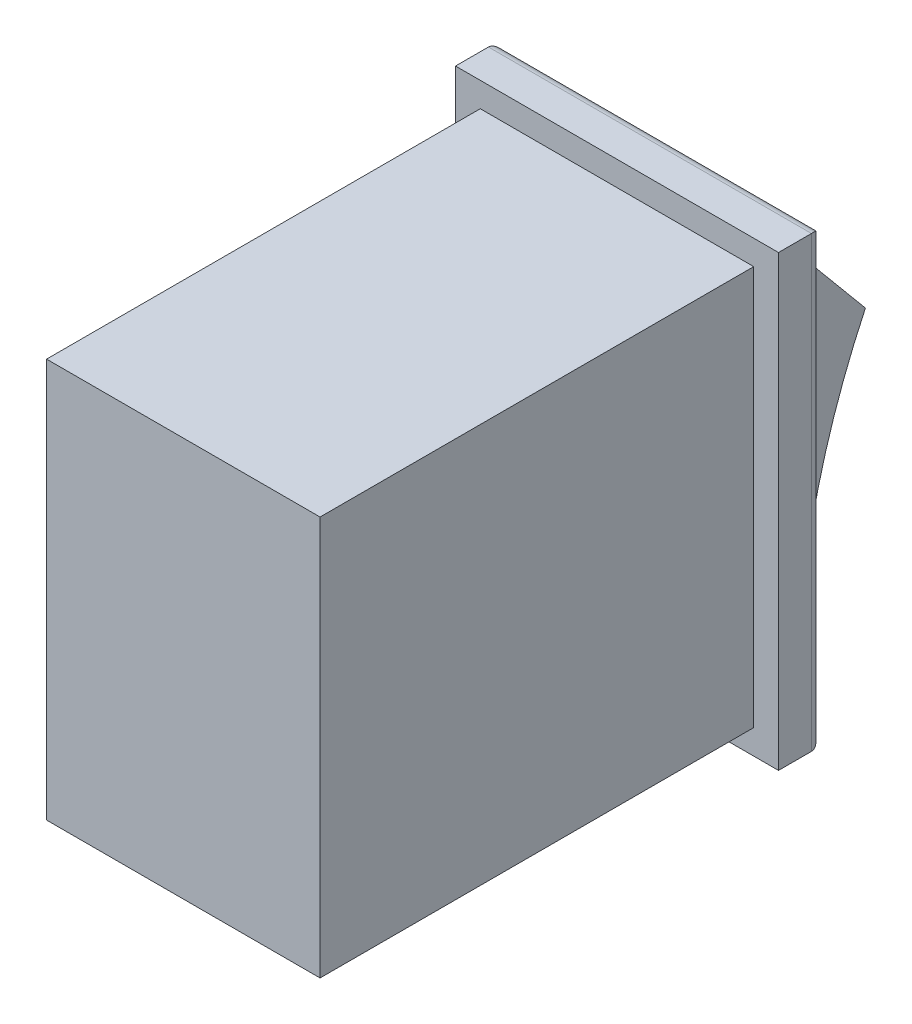
SolidWorks part; units mm, degrees
ref_plane "Front" through (0, 0, 0) normal (0, 0, 1) x (1, 0, 0)
ref_plane "Top" through (0, 0, 0) normal (0, 1, 0) x (1, 0, 0)
ref_plane "Right" through (0, 0, 0) normal (1, 0, 0) x (0, 0, -1)
sketch "Sketch1" plane through (0, 0, 0) normal (0, 0, 1) x (1, 0, 0)
  line L1 (0, 0) -> (12.7, 0)
  line L2 (0, 0) -> (0, -18.54)
  line L3 (0, -18.54) -> (12.7, -18.54)
  line L4 (12.7, 0) -> (12.7, -18.54)
  dimension "D1" = 12.7
  dimension "D2" = 18.54
extrude "Extrude1" add sketch "Sketch1" along normal blind 20.14
sketch "Sketch2" plane through (0, 0, 0) normal (0, 0, -1) x (-1, 0, 0)
  line L0 (0, 0) -> (0, -18.54) construction
  line L1 (-13.85, 1.1425) -> (1.15, 1.1425)
  line L2 (-13.85, 1.1425) -> (-13.85, -19.6875)
  line L3 (-13.85, -19.6875) -> (1.15, -19.6875)
  line L4 (1.15, 1.1425) -> (1.15, -19.6875)
  line L5 (-12.7, 0) -> (0, 0) construction
  dimension "D1" = 20.83
  dimension "D2" = 15
  dimension "D3" = 1.15
  dimension "D4" = 1.1425
extrude "Extrude2" add sketch "Sketch2" along normal blind 2.03
fillet "Fillet1" radius 0.5
sketch "Sketch3" plane through (0, 0, 0) normal (-1, 0, 0) x (0, 0, 1)
  line L0 (-2.03, -18.258) -> (-2.03, -0.4737)
  line L1 (-2.03, -19.1875) -> (-2.03, 0.6425) construction
  line L2 (-2.03, -0.4737) -> (-5.1861, -4.2582)
  arc A0 (-2.03, -18.258) -> (-5.1861, -4.2582) centre (-34.6576, -18.258) ccw
extrude "Extrude3" add sketch "Sketch3" against normal blind 12.7
